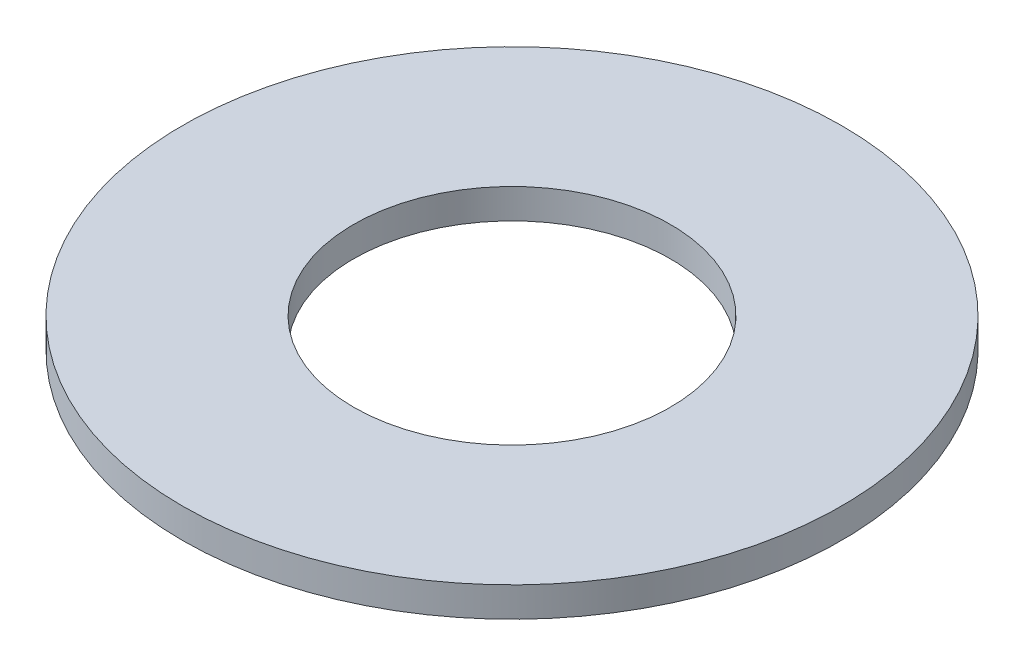
SolidWorks part; units mm, degrees
ref_plane "Front Plane" through (0, 0, 0) normal (0, 0, 1) x (1, 0, 0)
ref_plane "Top Plane" through (0, 0, 0) normal (0, 1, 0) x (1, 0, 0)
ref_plane "Right Plane" through (0, 0, 0) normal (1, 0, 0) x (0, 0, -1)
sketch "Sketch1" plane through (0, 0, 0) normal (0, 1, 0) x (1, 0, 0)
  circle A0 centre (0, 0) radius 41.275
  dimension "OD" = 82.55
extrude "Boss-Extrude1" add sketch "Sketch1" along normal blind 3.7338
sketch "Sketch5" plane through (0, 3.7338, 0) normal (0, 1, 0) x (-1, 0, 0)
  circle A0 centre (0, 0) radius 19.8374
  dimension "ID" = 39.6748
extrude "Cut-Extrude1" cut sketch "Sketch5" against normal through all
